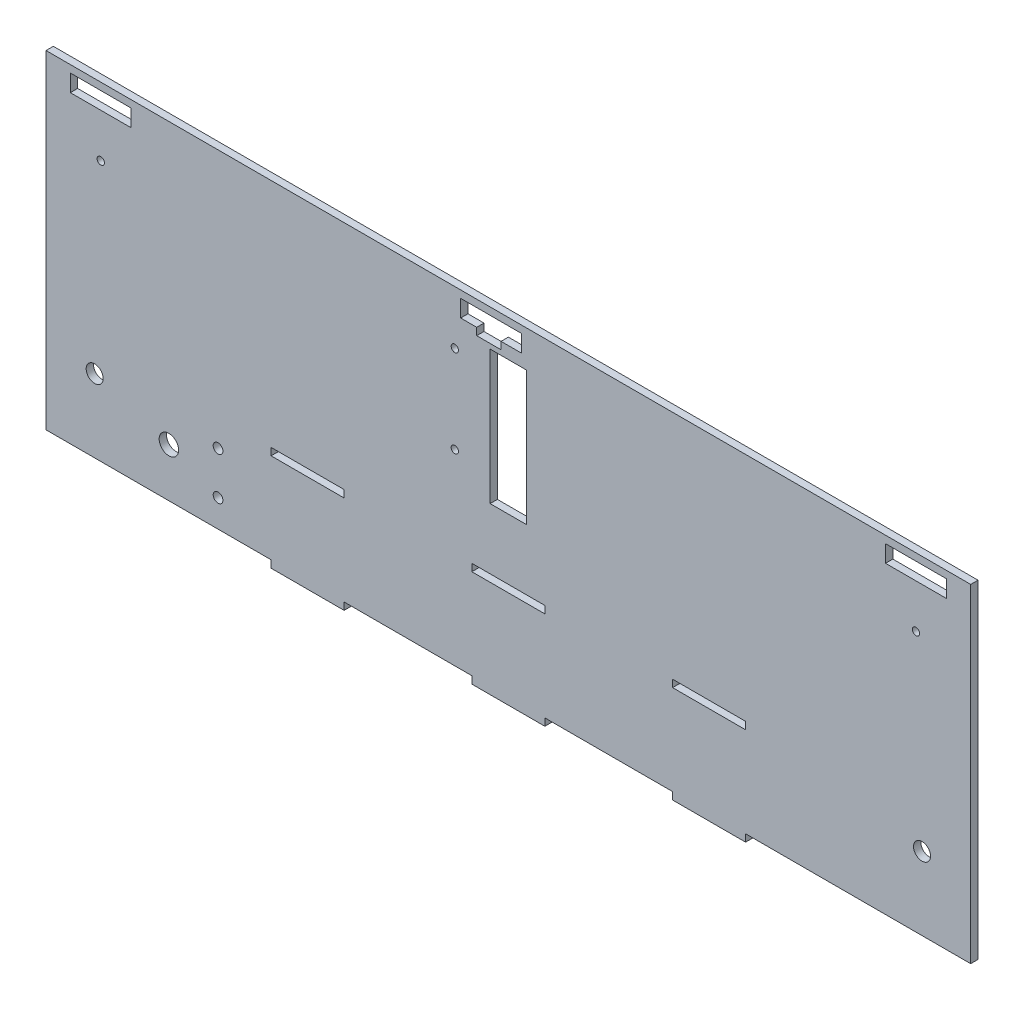
SolidWorks part; units mm, degrees
ref_plane "Alzado" through (0, 0, 0) normal (0, 0, 1) x (1, 0, 0)
ref_plane "Planta" through (0, 0, 0) normal (0, 1, 0) x (1, 0, 0)
ref_plane "Vista lateral" through (0, 0, 0) normal (1, 0, 0) x (0, 0, -1)
sketch "Croquis1" plane through (0, 0, 0) normal (0, 0, 1) x (1, 0, 0)
  line L0 (-190, -27.5) -> (190, -27.5) construction
  line L1 (-190, -67.5) -> (-97.5, -67.5)
  line L2 (-190, -67.5) -> (-190, 67.5)
  line L3 (-190, 67.5) -> (190, 67.5)
  line L4 (190, -67.5) -> (190, 67.5)
  line L5 (-190, -67.5) -> (190, 67.5) construction
  line L6 (-190, 67.5) -> (190, -67.5) construction
  line L7 (-190, 52.5) -> (190, 52.5) construction
  line L8 (67.5, -30.5) -> (97.5, -30.5)
  line L9 (-15, -30.5) -> (15, -30.5)
  line L10 (-15, -30.5) -> (-15, -27.5)
  line L11 (-15, -27.5) -> (15, -27.5)
  line L12 (15, -30.5) -> (15, -27.5)
  line L13 (-15, -30.5) -> (15, -27.5) construction
  line L14 (-15, -27.5) -> (15, -30.5) construction
  line L15 (67.5, -30.5) -> (67.5, -27.5)
  line L16 (67.5, -27.5) -> (97.5, -27.5)
  line L17 (97.5, -30.5) -> (97.5, -27.5)
  line L18 (67.5, -30.5) -> (97.5, -27.5) construction
  line L19 (67.5, -27.5) -> (97.5, -30.5) construction
  line L20 (-97.5, -30.5) -> (-67.5, -30.5)
  line L21 (-97.5, -30.5) -> (-97.5, -27.5)
  line L22 (-97.5, -27.5) -> (-67.5, -27.5)
  line L23 (-67.5, -30.5) -> (-67.5, -27.5)
  line L24 (-97.5, -30.5) -> (-67.5, -27.5) construction
  line L25 (-97.5, -27.5) -> (-67.5, -30.5) construction
  line L26 (0, 67.5) -> (0, -67.5) construction
  line L27 (-22, 67.5) -> (-22, -67.5) construction
  line L28 (-19.6, 64.5) -> (-19.6, 57.5)
  line L45 (-19.6, 57.5) -> (-13, 57.5)
  line L46 (-13, 57.5) -> (-13, 54.5)
  line L47 (-13, 54.5) -> (-3, 54.5)
  line L48 (-3, 54.5) -> (-3, 57.5)
  line L49 (-3, 57.5) -> (5.4, 57.5)
  line L50 (5.4, 57.5) -> (5.4, 64.5)
  line L51 (5.4, 64.5) -> (-19.6, 64.5)
  line L52 (0, 64.5) -> (0, 61) construction
  line L53 (-180, 64.5) -> (-180, 57.5)
  line L54 (-180, 57.5) -> (-173.4, 57.5)
  line L58 (-163.4, 57.5) -> (-155, 57.5)
  line L59 (-155, 57.5) -> (-155, 64.5)
  line L60 (-155, 64.5) -> (-180, 64.5)
  line L61 (-160.4, 64.5) -> (-160.4, 57.5) construction
  line L62 (155, 64.5) -> (155, 57.5)
  line L63 (155, 57.5) -> (161.6, 57.5)
  line L67 (171.6, 57.5) -> (180, 57.5)
  line L68 (180, 57.5) -> (180, 64.5)
  line L69 (180, 64.5) -> (155, 64.5)
  line L70 (174.6, 64.5) -> (174.6, 57.5) construction
  line L71 (-160.4, 67.5) -> (-160.4, 52.5) construction
  line L72 (174.6, 67.5) -> (174.6, 52.5) construction
  line L73 (-97.5, -70.5) -> (-67.5, -70.5)
  line L74 (-97.5, -70.5) -> (-97.5, -67.5)
  line L76 (-67.5, -70.5) -> (-67.5, -67.5)
  line L77 (-15, -70.5) -> (15, -70.5)
  line L78 (-15, -70.5) -> (-15, -67.5)
  line L80 (15, -70.5) -> (15, -67.5)
  line L81 (67.5, -70.5) -> (97.5, -70.5)
  line L82 (67.5, -70.5) -> (67.5, -67.5)
  line L84 (97.5, -70.5) -> (97.5, -67.5)
  line L85 (-67.5, -67.5) -> (-15, -67.5)
  line L86 (15, -67.5) -> (67.5, -67.5)
  line L87 (97.5, -67.5) -> (190, -67.5)
  line L88 (-173.4, 57.5) -> (-163.4, 57.5)
  line L89 (-7.5, 52.5) -> (7.5, 52.5)
  line L90 (-7.5, 52.5) -> (-7.5, -2.5)
  line L91 (-7.5, -2.5) -> (7.5, -2.5)
  line L92 (7.5, 52.5) -> (7.5, -2.5)
  line L93 (161.6, 57.5) -> (171.6, 57.5)
  circle A0 centre (-22, 45.5) radius 1.5
  circle A1 centre (-22, 9.5) radius 1.5
  circle A2 centre (-170, -37.5) radius 3.5
  circle A3 centre (-139.5, -47.5) radius 4
  circle A4 centre (-119.3, -38.75) radius 2
  circle A5 centre (-119.3, -56.25) radius 2
  circle A6 centre (170, -37.5) radius 3.5
  circle A7 centre (-167.5, 39.5) radius 1.5
  circle A8 centre (167.5, 39.5) radius 1.5
  point P0 (0, 0)
  point P10 (0, -29)
  point P15 (82.5, -29)
  point P20 (-82.5, -29)
  point P91 (167.5, 64.5)
  point P92 (-167.5, 64.5)
  dimension "D11" = 3
  dimension "D13" = 3
  dimension "D42" = 7
  dimension "D45" = 8
  dimension "D47" = 4
  dimension "D48" = 4
  dimension "D53" = 7
  dimension "D23" = 3
  dimension "D32" = 3
  dimension "D1" = 135
  dimension "400" = 380
  dimension "D2" = 40
  dimension "D3" = 15
  dimension "D4" = 3
  dimension "D5" = 30
  dimension "D6" = 3
  dimension "D7" = 3
  dimension "D8" = 82.5
  dimension "D9" = 82.5
  dimension "D10" = 22
  dimension "D12" = 7
  dimension "D14" = 37
  dimension "D15" = 3
  dimension "D16" = 25
  dimension "D17" = 7
  dimension "D18" = 10
  dimension "D19" = 3
  dimension "D20" = 19.6
  dimension "D21" = 25
  dimension "D22" = 7
  dimension "D24" = 25
  dimension "D25" = 19.6
  dimension "D26" = 25
  dimension "D27" = 7
  dimension "D28" = 10
  dimension "D29" = 10
  dimension "D30" = 19.6
  dimension "D31" = 3
  dimension "D33" = 3
  dimension "D34" = 25
  dimension "D35" = 3
  dimension "D36" = 3
  dimension "D39" = 15
  dimension "D40" = 55
  dimension "D41" = 7.5
  dimension "D43" = 20
  dimension "D44" = 30
  dimension "D46" = 50.5
  dimension "D49" = 17.5
  dimension "D50" = 11.25
  dimension "D51" = 70.7
  dimension "D52" = 20
  dimension "D54" = 20
  dimension "D55" = 30
extrude "Saliente-Extruir4" add sketch "Croquis1" along normal blind 3
